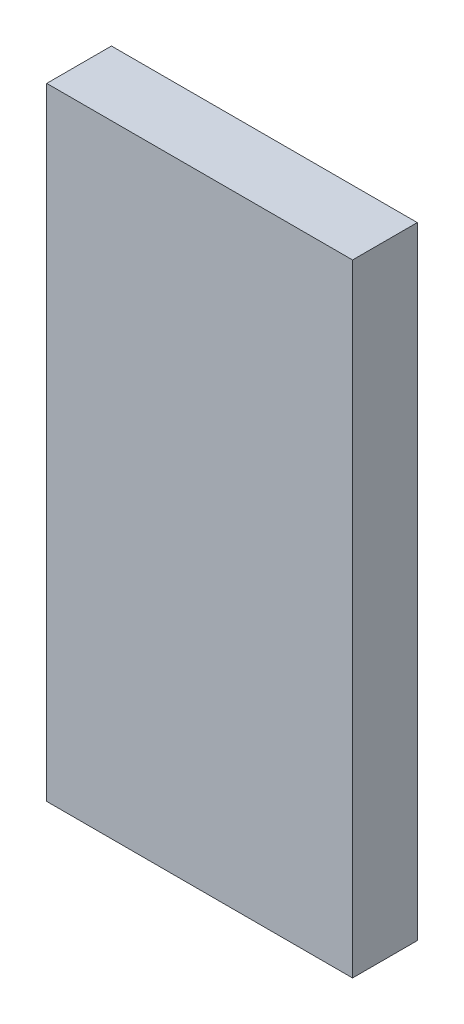
SolidWorks part; units mm, degrees
material "Balsa"
ref_plane "Front Plane" through (0, 0, 0) normal (0, 0, 1) x (1, 0, 0)
ref_plane "Top Plane" through (0, 0, 0) normal (0, 1, 0) x (1, 0, 0)
ref_plane "Right Plane" through (0, 0, 0) normal (1, 0, 0) x (0, 0, -1)
sketch "Sketch1" plane through (0, 0, 0) normal (0, 0, 1) x (1, 0, 0)
  line L1 (0, 0) -> (30, 0)
  line L2 (0, 0) -> (0, 61)
  line L3 (0, 61) -> (30, 61)
  line L4 (30, 0) -> (30, 61)
  dimension "D1" = 30
  dimension "D2" = 61
extrude "Boss-Extrude1" add sketch "Sketch1" along normal blind 6.35
